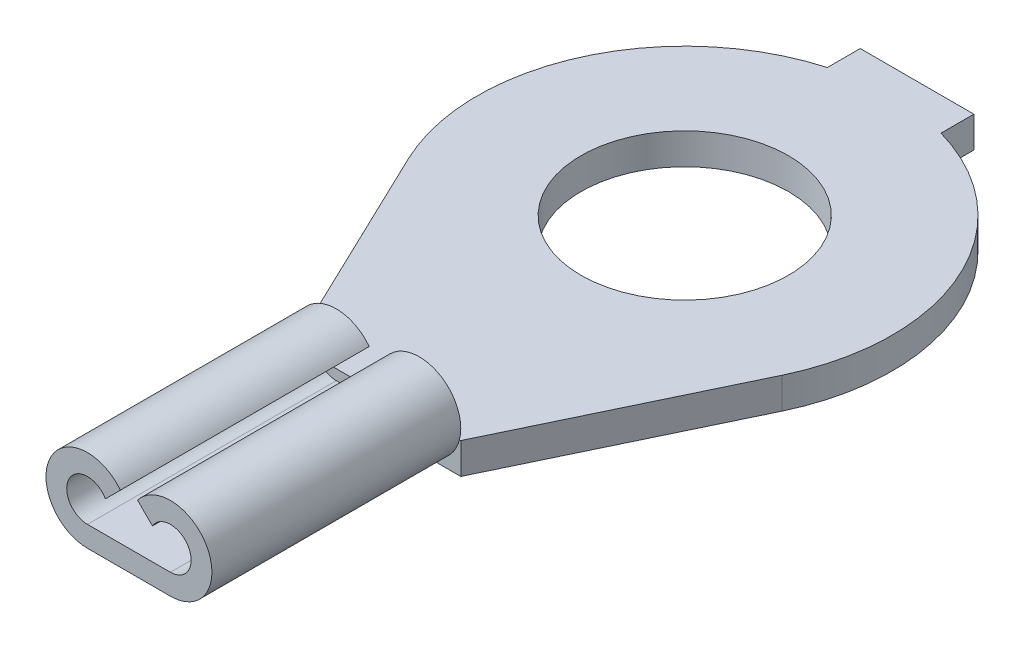
SolidWorks part; units mm, degrees
ref_plane "Front Plane" through (0, 0, 0) normal (0, 0, 1) x (1, 0, 0)
ref_plane "Top Plane" through (0, 0, 0) normal (0, 1, 0) x (1, 0, 0)
ref_plane "Right Plane" through (0, 0, 0) normal (1, 0, 0) x (0, 0, -1)
sketch "Sketch1" plane through (0, 0, 0) normal (0, 1, 0) x (1, 0, 0)
  line L0 (0, 0) -> (0, 7.8819) construction
  line L1 (-0.696, 2.4428) -> (-0.696, 2.8455)
  line L2 (-0.696, 2.8455) -> (0.696, 2.8455)
  line L3 (0.696, 2.4428) -> (0.696, 2.8455)
  line L4 (-1.016, -6.8065) -> (1.016, -6.8065)
  line L5 (-1.016, -6.8065) -> (-1.016, -3.7585)
  line L6 (-1.016, -3.7585) -> (-2.2908, -1.0973)
  line L7 (1.016, -3.7585) -> (2.2908, -1.0973)
  line L8 (1.016, -6.8065) -> (1.016, -3.7585)
  circle A0 centre (0, 0) radius 1.27
  arc A1 (-0.696, 2.4428) -> (-2.2908, -1.0973) centre (0, 0) ccw
  arc A2 (2.2908, -1.0973) -> (0.696, 2.4428) centre (0, 0) ccw
  circle A3 centre (0, 0) radius 2.54 construction
  point P10 (0, 2.8455)
  point P11 (2.794, 0)
  point P20 (0, -6.8065)
  dimension "D1" = 2.54
  dimension "D3" = 9.652
  dimension "D4" = 1.016
  dimension "D5" = 3.048
  dimension "D6" = 0.4027
  dimension "D2" = 1.27
extrude "Boss-Extrude1" add sketch "Sketch1" along normal blind 0.381
sketch "Sketch2" plane through (0, 0.381, 0) normal (0, 1, 0) x (1, 0, 0)
  line L0 (-1.016, -3.7585) -> (-1.016, -6.8065) construction
  line L1 (1.016, -6.8065) -> (1.016, -3.7585) construction
  line L2 (-1.016, -6.8065) -> (1.016, -6.8065) construction
  line L3 (-1.016, -3.7585) -> (-1.016, -6.8065)
  line L4 (1.016, -6.8065) -> (1.016, -3.7585)
  line L5 (-1.016, -6.8065) -> (1.016, -6.8065)
  line L6 (-1.016, -3.7585) -> (1.016, -3.7585)
extrude "Boss-Extrude2" add sketch "Sketch2" along normal blind 0.635
sketch "Sketch3" plane through (0, 0, 6.8065) normal (0, 0, 1) x (1, 0, 0)
  line L0 (0, 0) -> (0, 2.7928) construction
  line L1 (0.508, 0) -> (1.016, 0)
  line L2 (-1.016, 1.016) -> (1.016, 1.016) construction
  line L3 (-1.016, 1.016) -> (-1.016, 0) construction
  line L4 (-1.016, 0) -> (1.016, 0) construction
  line L5 (1.016, 1.016) -> (1.016, 0) construction
  line L6 (-1.016, 1.016) -> (1.016, 1.016)
  line L7 (-1.016, 1.016) -> (-1.016, 0)
  line L8 (-1.016, 0) -> (-0.508, 0)
  line L9 (1.016, 1.016) -> (1.016, 0)
  line L10 (-1.016, 0.508) -> (1.0798, 0.508) construction
  line L11 (-0.508, 0.254) -> (0.508, 0.254)
  line L12 (-0.288, 0.635) -> (-0.1053, 0.8177)
  line L14 (0.288, 0.635) -> (0.1053, 0.8177)
  arc A0 (-0.288, 0.635) -> (-0.508, 0.254) centre (-0.508, 0.508) ccw
  arc A1 (-0.1053, 0.8177) -> (-0.508, 0) centre (-0.508, 0.508) ccw
  arc A2 (0.288, 0.635) -> (0.508, 0.254) centre (0.508, 0.508) cw
  arc A3 (0.1053, 0.8177) -> (0.508, 0) centre (0.508, 0.508) cw
  circle A5 centre (-0.508, 0.508) radius 0.508 construction
  circle A6 centre (-0.508, 0.508) radius 0.254 construction
  point P15 (-0.0222, 0.6565)
  point P21 (0.254, 0.508)
  point P22 (-0.254, 0.508)
  point P23 (-0.2651, 0.5823)
  line M1 (-1.016, 0) -> (1.016, 0)
  line M2 (1.016, 0) -> (1.016, 1.016)
  line M3 (1.016, 1.016) -> (-1.016, 1.016)
  line M4 (-1.016, 1.016) -> (-1.016, 0)
  dimension "D1" = 0.508
  dimension "D2" = 0.508
  dimension "D3" = 0.254
extrude "Cut-Extrude1" cut sketch "Sketch3" against normal up to vertex contours A1 L6 M4 | A1 L7 M1 | A0 | A1 A3 L6 | A3 L9 M3 | A3 M2 M1 | A2
